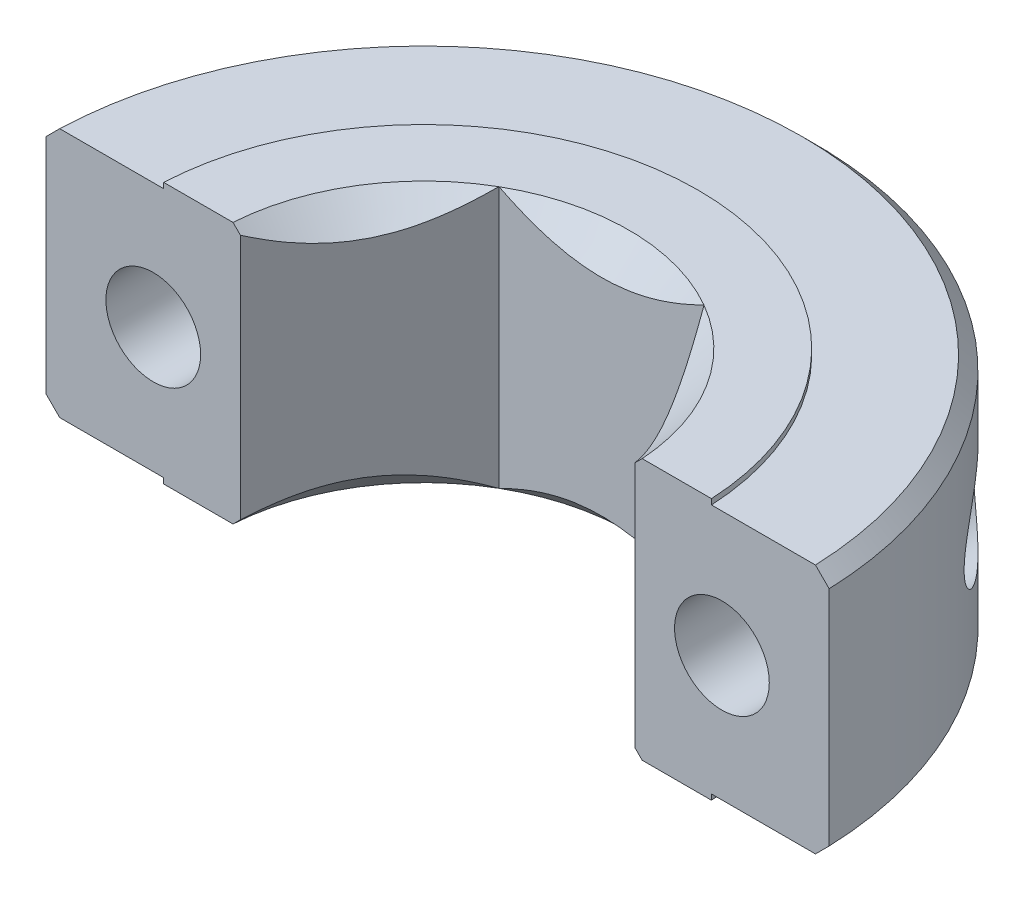
SolidWorks part; units mm, degrees
ref_plane "Front Plane" through (0, 0, 0) normal (0, 0, 1) x (1, 0, 0)
ref_plane "Top Plane" through (0, 0, 0) normal (0, 1, 0) x (1, 0, 0)
ref_plane "Right Plane" through (0, 0, 0) normal (1, 0, 0) x (0, 0, -1)
ref_plane "Plane3" through (0, 4.7625, 0) normal (0, 1, 0) x (1, 0, 0)
sketch "Sketch19" plane through (0, 4.7625, 0) normal (0, 1, 0) x (1, 0, 0)
  line L0 (-14.2787, 0.5) -> (-7.1903, 0.5)
  line L1 (-7.1903, 0.5) -> (-3.7395, 6.477)
  line L2 (-3.7395, 6.477) -> (3.7395, 6.477)
  line L3 (3.7395, 6.477) -> (7.1903, 0.5)
  line L4 (7.1903, 0.5) -> (14.2787, 0.5)
  arc A0 (14.2787, 0.5) -> (-14.2787, 0.5) centre (0, 0) ccw
  dimension "D1" = 14.2875
  dimension "D2" = 7.0884
  dimension "D3" = 10.5393
  dimension "D4" = 14.2787
  dimension "D5" = 18.0182
  dimension "D6" = 21.4691
  dimension "D7" = 5.977
extrude "Boss-Extrude1" add sketch "Sketch19" against normal blind 9.525
ref_plane "Plane4" through (0, 0, 0) normal (-0.8658, 0, -0.5004) x (0, -1, 0)
sketch "Sketch20" plane through (0, 0, 0) normal (-0.8658, 0, -0.5004) x (0, -1, 0)
  line L0 (4.7625, 0) -> (3.7625, 0)
  line L1 (3.7625, 0) -> (3.7625, -6.477)
  line L2 (3.7625, -6.477) -> (4.7625, -7.477)
  line L3 (4.7625, -7.477) -> (4.7625, 0)
  line L4 (4.7625, 0) -> (3.7625, 0) construction
  dimension "D1" = 1
  dimension "D2" = 6.477
  dimension "D3" = 7.477
revolve "Cut-Revolve1" cut sketch "Sketch20" angle 360 about L4
ref_plane "Plane5" through (0, 0, 0) normal (0.0669, 0, 0.9978) x (0, 1, 0)
sketch "Sketch21" plane through (0, 0, 0) normal (0.0669, 0, 0.9978) x (0, 1, 0)
  line L0 (4.7625, -7.477) -> (4.7625, 0)
  line L1 (4.7625, 0) -> (3.7625, 0)
  line L2 (3.7625, 0) -> (3.7625, -6.477)
  line L3 (3.7625, -6.477) -> (4.7625, -7.477)
  line L4 (4.7625, 0) -> (3.7625, 0) construction
  dimension "D1" = 1
  dimension "D2" = 6.477
  dimension "D3" = 7.477
revolve "Cut-Revolve2" cut sketch "Sketch21" angle 360 about L4
sketch "Sketch26" plane through (0, 4.7625, 0) normal (0, 1, 0) x (1, 0, 0)
  line L0 (-14.2787, 0.5) -> (-9.9875, 0.5)
  line L1 (9.9875, 0.5) -> (14.2787, 0.5)
  arc A0 (-9.9875, 0.5) -> (9.9875, 0.5) centre (0, 0) cw
  arc A1 (14.2787, 0.5) -> (-14.2787, 0.5) centre (0, 0) ccw
  dimension "D1" = 10
  dimension "D2" = 14.2875
  dimension "D3" = 4.2913
extrude "Cut-Extrude7" cut sketch "Sketch26" against normal blind 0.2
sketch "Sketch27" plane through (0, -4.7625, 0) normal (0, -1, 0) x (1, 0, 0)
  line L0 (-9.9875, -0.5) -> (-14.2787, -0.5)
  line L1 (14.2787, -0.5) -> (9.9875, -0.5)
  line L2 (7.4603, -0.5) -> (14.2787, -0.5) construction
  arc A0 (9.9875, -0.5) -> (-9.9875, -0.5) centre (0, 0) cw
  arc A1 (-14.2787, -0.5) -> (14.2787, -0.5) centre (0, 0) ccw
  dimension "D1" = 10
  dimension "D2" = 14.2875
  dimension "D3" = 3.7355
  dimension "D4" = 13.723
  dimension "D5" = 0.5
extrude "Cut-Extrude8" cut sketch "Sketch27" against normal blind 0.2
hole_wizard "#29 (0.136) Diameter Hole4" positions "Sketch29" profile "Sketch28" hole size "#29" standard "ANSI Inch"
sketch "Sketch29" plane through (0, 0, -0.5) normal (0, 0, 1) x (1, 0, 0)
  point P0 (-10.3682, 0)
  point P1 (10.3682, 0)
sketch "Sketch28" plane through (-10.3682, 0, -0.5) normal (1, 0, 0) x (0, -1, 0)
  line L0 (0, 0) -> (0, 13.7875)
  line L1 (0, 13.7875) -> (1.7272, 13.7875)
  line L2 (1.7272, 13.7875) -> (1.7272, 0)
  line L5 (1.7272, 0) -> (0, 0)
  line L11 (0, -6.35) -> (0, 107.95) construction
  dimension "Thru Hole Dia." = 3.4544
  dimension "Thru Hole Depth" = 13.7875
chamfer "Chamfer4" distance 0.5 angle 45 2 edges at (0, 4.5625, -14.2875) (0, -4.5625, -14.2875)
